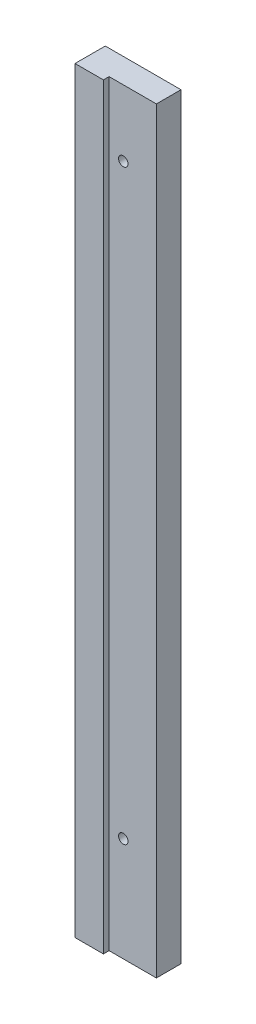
SolidWorks part; units mm, degrees
material "Литая легированная сталь"
ref_plane "Front" through (0, 0, 0) normal (0, 0, 1) x (1, 0, 0)
ref_plane "Top" through (0, 0, 0) normal (0, 1, 0) x (1, 0, 0)
ref_plane "Right" through (0, 0, 0) normal (1, 0, 0) x (0, 0, -1)
sketch "Sketch1" plane through (0, 0, 0) normal (0, 0, 1) x (1, 0, 0)
  line L1 (-20, 200) -> (20, 200)
  line L2 (-20, 200) -> (-20, -200)
  line L3 (-20, -200) -> (20, -200)
  line L4 (20, 200) -> (20, -200)
  line L5 (-20, 200) -> (20, -200) construction
  line L6 (-20, -200) -> (20, 200) construction
  point P0 (0, 0)
  dimension "D1" = 400
  dimension "D2" = 40
extrude "Extrude1" add sketch "Sketch1" along normal blind 16
sketch "Sketch2" plane through (0, -200, 0) normal (0, -1, 0) x (1, 0, 0)
  line L0 (-20, 16) -> (20, 16) construction
  line L1 (-5, 16) -> (20, 16)
  line L2 (-5, 16) -> (-5, 13)
  line L3 (-5, 13) -> (20, 13)
  line L4 (20, 16) -> (20, 13)
  line L5 (20, 16) -> (20, 0) construction
  dimension "D1" = 25
  dimension "D2" = 3
extrude "Extrude2" cut sketch "Sketch2" against normal up to next
hole_wizard "M6 Tapped Hole1" positions "Sketch5" profile "Sketch6" tap size "M6" standard "DIN" end condition through all
sketch "Sketch5" plane through (0, 0, 0) normal (0, 0, -1) x (-1, 0, 0)
  point P0 (-2.5, 165)
  point P3 (-2.5, -145)
sketch "Sketch6" plane through (2.5, 165, 0) normal (1, 0, 0) x (0, 1, 0)
  line L0 (0, 0) -> (0, 16)
  line L1 (0, 16) -> (2.5, 16)
  line L2 (2.5, 16) -> (2.5, 0)
  line L5 (2.5, 0) -> (0, 0)
  line L11 (0, -6.35) -> (0, 107.95) construction
  dimension "Диаметр проходного сверла" = 5
  dimension "Глубина проходного сверла" = 16
cosmetic thread "Cosmetic Thread8" parameters "D2"=6
cosmetic thread "Cosmetic Thread9" parameters "D2"=6
